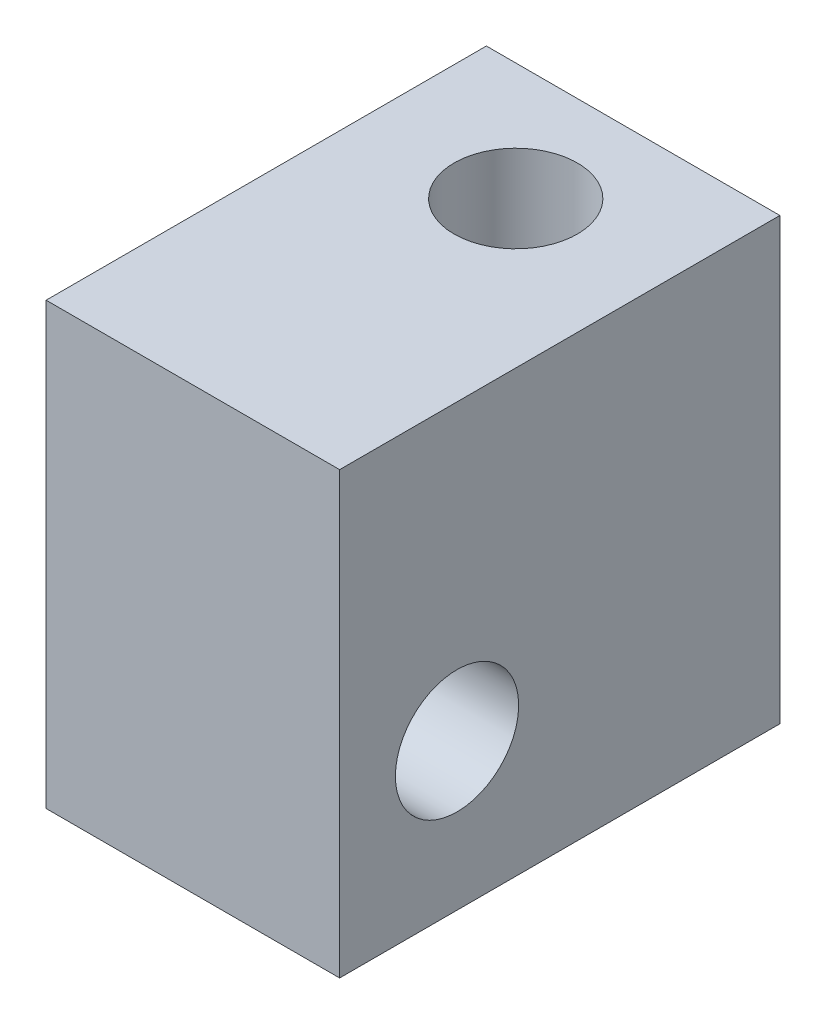
SolidWorks part; units mm, degrees
material "ABS"
ref_plane "Front Plane" through (0, 0, 0) normal (0, 0, 1) x (1, 0, 0)
ref_plane "Top Plane" through (0, 0, 0) normal (0, 1, 0) x (1, 0, 0)
ref_plane "Right Plane" through (0, 0, 0) normal (1, 0, 0) x (0, 0, -1)
sketch "Sketch1" plane through (0, 0, 0) normal (0, 0, 1) x (1, 0, 0)
  line L1 (-5, -7.5) -> (5, -7.5)
  line L2 (-5, -7.5) -> (-5, 7.5)
  line L3 (-5, 7.5) -> (5, 7.5)
  line L4 (5, -7.5) -> (5, 7.5)
  line L5 (-5, -7.5) -> (5, 7.5) construction
  line L6 (-5, 7.5) -> (5, -7.5) construction
  point P0 (0, 0)
  dimension "D1" = 10
  dimension "D2" = 15
extrude "Boss-Extrude1" add sketch "Sketch1" along normal blind 15
hole_wizard "M5x0.8 Tapped Hole1" positions "Sketch3" profile "Sketch5" tap size "M5x0.8" standard "ANSI Metric" end condition through all
sketch "Sketch3" plane through (0, 7.5, 0) normal (0, 1, 0) x (1, 0, 0)
  line L1 (5, 0) -> (-5, 0) construction
  point P0 (0, -4)
  dimension "D1" = 4
sketch "Sketch5" plane through (0, 7.5, 4) normal (1, 0, 0) x (0, 0, 1)
  line L0 (0, 0) -> (0, 15)
  line L1 (0, 15) -> (2.1, 15)
  line L2 (2.1, 15) -> (2.1, 0)
  line L5 (2.1, 0) -> (0, 0)
  line L11 (0, -6.35) -> (0, 107.95) construction
  dimension "Thru Tap Drill Dia." = 4.2
  dimension "Thru Tap Drill Depth" = 15
hole_wizard "M5x0.8 Tapped Hole2" positions "Sketch6" profile "Sketch7" tap size "M5x0.8" standard "ANSI Metric" end condition through all
sketch "Sketch6" plane through (-5, 0, 0) normal (-1, 0, 0) x (0, 0, 1)
  line L0 (15, 7.5) -> (15, -7.5) construction
  line L1 (15, -7.5) -> (0, -7.5) construction
  point P0 (11, -2.5)
  dimension "D1" = 4
  dimension "D2" = 5
sketch "Sketch7" plane through (-5, -2.5, 11) normal (0, 1, 0) x (0, 0, 1)
  line L0 (0, 0) -> (0, 10)
  line L1 (0, 10) -> (2.1, 10)
  line L2 (2.1, 10) -> (2.1, 0)
  line L5 (2.1, 0) -> (0, 0)
  line L11 (0, -6.35) -> (0, 107.95) construction
  dimension "Thru Tap Drill Dia." = 4.2
  dimension "Thru Tap Drill Depth" = 10
